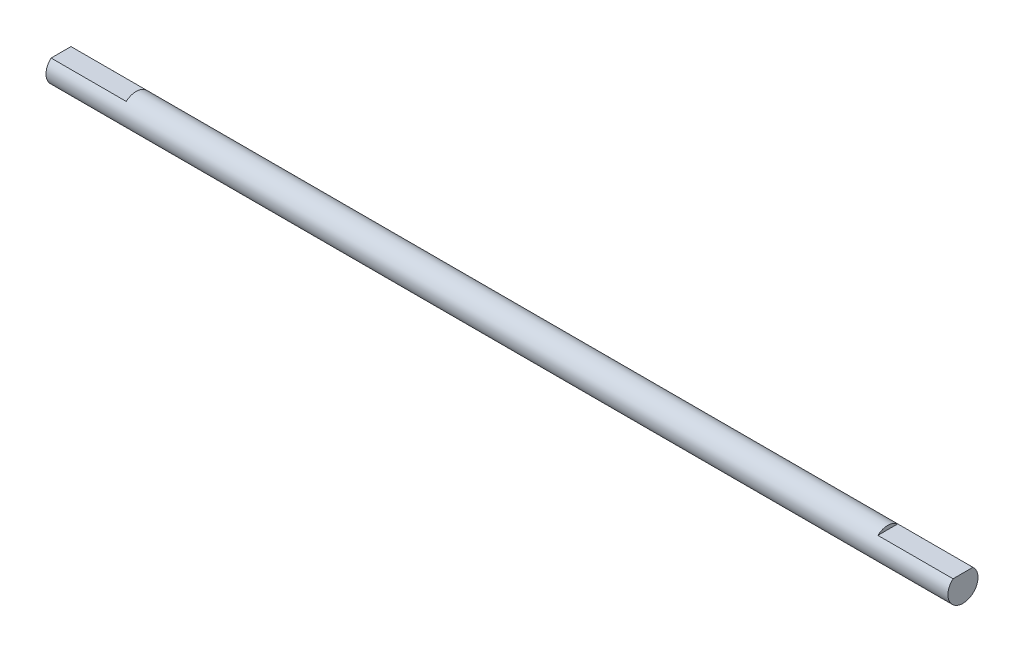
SolidWorks part; units mm, degrees
material "Plain Carbon Steel"
ref_plane "Front Plane" through (0, 0, 0) normal (0, 0, 1) x (1, 0, 0)
ref_plane "Top Plane" through (0, 0, 0) normal (0, 1, 0) x (1, 0, 0)
ref_plane "Right Plane" through (0, 0, 0) normal (1, 0, 0) x (0, 0, -1)
sketch "Sketch1" plane through (0, 0, 0) normal (1, 0, 0) x (0, 0, -1)
  line L0 (-1.3229, 1.5) -> (1.3229, 1.5)
  arc A0 (-1.3229, 1.5) -> (1.3229, 1.5) centre (0, 0) ccw
  dimension "D1" = 4
  dimension "D2" = 1.5
extrude "Boss-Extrude1" add sketch "Sketch1" along normal mid plane 120
sketch "Sketch2" plane through (0, 0, 0) normal (1, 0, 0) x (0, 0, -1)
  circle A0 centre (0, 0) radius 2
  arc A1 (-1.3229, 1.5) -> (1.3229, 1.5) centre (0, 0) ccw construction
extrude "Boss-Extrude2" add sketch "Sketch2" along normal mid plane 100
